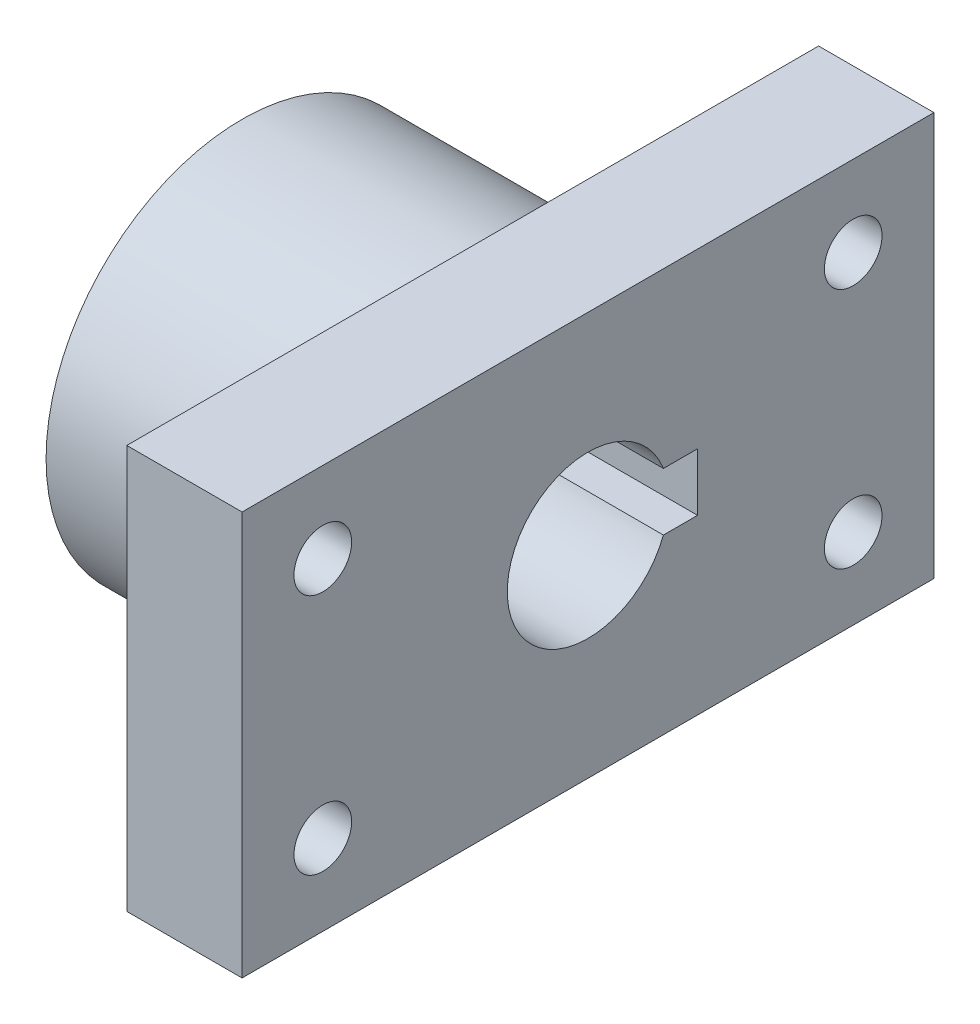
SolidWorks part; units mm, degrees
material "Plain Carbon Steel"
ref_plane "Front Plane" through (0, 0, 0) normal (0, 0, 1) x (1, 0, 0)
ref_plane "Top Plane" through (0, 0, 0) normal (0, 1, 0) x (1, 0, 0)
ref_plane "Right Plane" through (0, 0, 0) normal (1, 0, 0) x (0, 0, -1)
sketch "Sketch1" plane through (0, 0, 0) normal (1, 0, 0) x (0, 0, -1)
  line L1 (30, -17.5) -> (-30, -17.5)
  line L2 (30, -17.5) -> (30, 17.5)
  line L3 (30, 17.5) -> (-30, 17.5)
  line L4 (-30, -17.5) -> (-30, 17.5)
  line L5 (30, -17.5) -> (-30, 17.5) construction
  line L6 (30, 17.5) -> (-30, -17.5) construction
  point P0 (0, 0)
  dimension "D1" = 60
  dimension "D2" = 35
extrude "Boss-Extrude1" add sketch "Sketch1" along normal blind 30
sketch "Sketch2" plane through (30, 0, 0) normal (1, 0, 0) x (0, 0, -1)
  line L7 (4.5, -2.5) -> (9.5, -2.5)
  line L8 (4.5, -2.5) -> (4.5, 2.5)
  line L9 (4.5, 2.5) -> (9.5, 2.5)
  line L10 (9.5, -2.5) -> (9.5, 2.5)
  line L11 (4.5, -2.5) -> (9.5, 2.5) construction
  line L12 (4.5, 2.5) -> (9.5, -2.5) construction
  circle A0 centre (0, 0) radius 7
  point P3 (0, 7)
  point P8 (7, 0)
  dimension "D1" = 14
  dimension "D2" = 5
extrude "Cut-Extrude1" cut sketch "Sketch2" against normal through all contours L9 A0 L7 L8 | L7 A0 L9 L8 | A0 L7 L10 L9
hole_wizard "Ø5.0 (5) Diameter Hole1" positions "Sketch5" profile "Sketch4" hole size "Ø5.0" standard "ISO" end condition through all
sketch "Sketch5" plane through (0, 0, 0) normal (-1, 0, 0) x (0, 0, 1)
  line L0 (-23, 17.5) -> (-23, 10.5) construction
  line L1 (-30, 17.5) -> (30, 17.5) construction
  line L2 (-23, 10.5) -> (-23, -10.5) construction
  line L3 (-23, -10.5) -> (-23, -17.5) construction
  line L4 (30, -17.5) -> (-30, -17.5) construction
  line L6 (-30, -17.5) -> (-30, 17.5) construction
  point P0 (-23, 10.5)
  point P2 (-23, -10.5)
  dimension "D1" = 7
  dimension "D2" = 7
sketch "Sketch4" plane through (0, 10.5, -23) normal (0, 1, 0) x (0, 0, 1)
  line L0 (0, 0) -> (0, 30)
  line L1 (0, 30) -> (2.5, 30)
  line L2 (2.5, 30) -> (2.5, 0)
  line L5 (2.5, 0) -> (0, 0)
  line L11 (0, -6.35) -> (0, 107.95) construction
  dimension "Thru Hole Dia." = 5
  dimension "Thru Hole Depth" = 30
mirror "Mirror1" about plane through (0, 0, 0) normal (0, 0, 1) of "Ø5.0 (5) Diameter Hole1"
sketch "Sketch6" plane through (0, 0, 0) normal (-1, 0, 0) x (0, 0, 1)
  line L1 (-30, 17.5) -> (30, 17.5)
  line L2 (-30, 17.5) -> (-30, -17.5)
  line L3 (-30, -17.5) -> (30, -17.5)
  line L4 (30, 17.5) -> (30, -17.5)
  circle A0 centre (0, 0) radius 17
  dimension "D1" = 34
extrude "Cut-Extrude2" cut sketch "Sketch6" against normal offset from surface (20 mm away) 10 up to face at (30, 0, 0)
